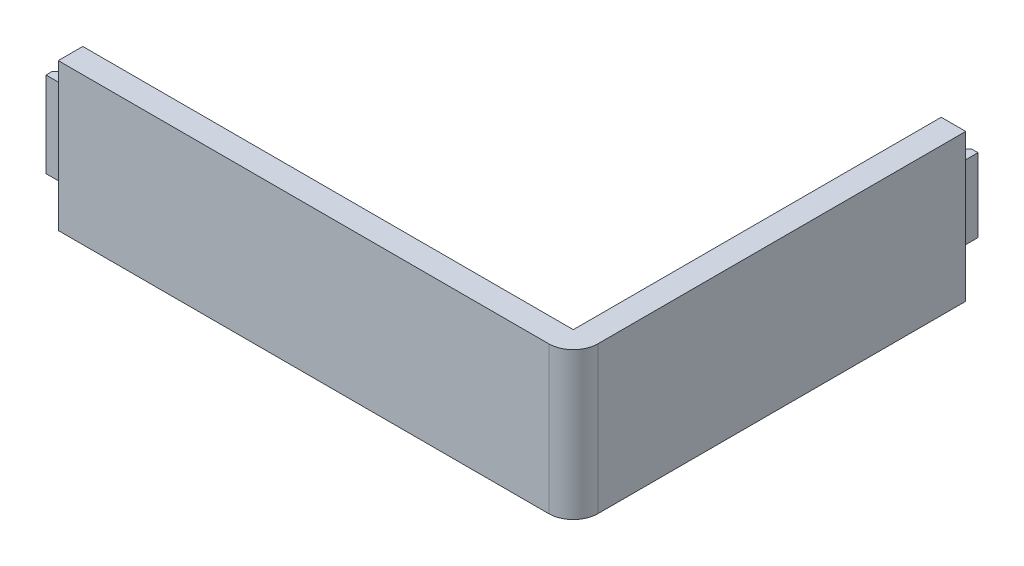
SolidWorks part; units mm, degrees
ref_plane "Front Plane" through (0, 0, 0) normal (0, 0, 1) x (1, 0, 0)
ref_plane "Top Plane" through (0, 0, 0) normal (0, 1, 0) x (1, 0, 0)
ref_plane "Right Plane" through (0, 0, 0) normal (1, 0, 0) x (0, 0, -1)
sketch "Sketch1" plane through (0, 0, 0) normal (0, 1, 0) x (1, 0, 0)
  line L1 (0, 0) -> (105, 0)
  line L2 (0, 0) -> (0, 5)
  line L3 (0, 5) -> (100, 5)
  line L6 (105, 0) -> (105, 80)
  line L7 (105, 80) -> (100, 80)
  line L8 (100, 5) -> (100, 80)
  dimension "D1" = 100
  dimension "D2" = 5
  dimension "D3" = 5
  dimension "D4" = 75
extrude "Boss-Extrude1" add sketch "Sketch1" along normal blind 30
sketch "Sketch2" plane through (0, 0, 0) normal (-1, 0, 0) x (0, 0, 1)
  line L0 (-5, 30) -> (-5, 0) construction
  line L1 (-5, 23.7124) -> (-2.5, 23.7124)
  line L2 (-5, 23.7124) -> (-5, 6.2876)
  line L3 (-5, 6.2876) -> (-2.5, 6.2876)
  line L4 (-2.5, 23.7124) -> (-2.5, 6.2876)
  line L5 (-5, 0) -> (0, 0) construction
  point P6 (-5, 15)
  dimension "D1" = 2.5
  dimension "D2" = 17.4247
  dimension "D3" = 15
extrude "Boss-Extrude2" add sketch "Sketch2" along normal blind 5
chamfer "Chamfer1" distance 1.25 angle 45 1 edges at (-5, 15, -5)
sketch "Sketch3" plane through (0, 0, -80) normal (0, 0, -1) x (-1, 0, 0)
  line L0 (-100, 30) -> (-100, 0) construction
  line L1 (-100, 22.5) -> (-102.5, 22.5)
  line L2 (-100, 22.5) -> (-100, 7.5)
  line L3 (-100, 7.5) -> (-102.5, 7.5)
  line L4 (-102.5, 22.5) -> (-102.5, 7.5)
  line L5 (-105, 0) -> (-100, 0) construction
  point P6 (-100, 15)
  dimension "D1" = 2.5
  dimension "D2" = 15
  dimension "D3" = 15
extrude "Boss-Extrude3" add sketch "Sketch3" along normal blind 5
chamfer "Chamfer2" distance 1.25 angle 45 1 edges at (100, 15, -85)
fillet "Fillet1" radius 5 1 edges at (105, 15, 0)
